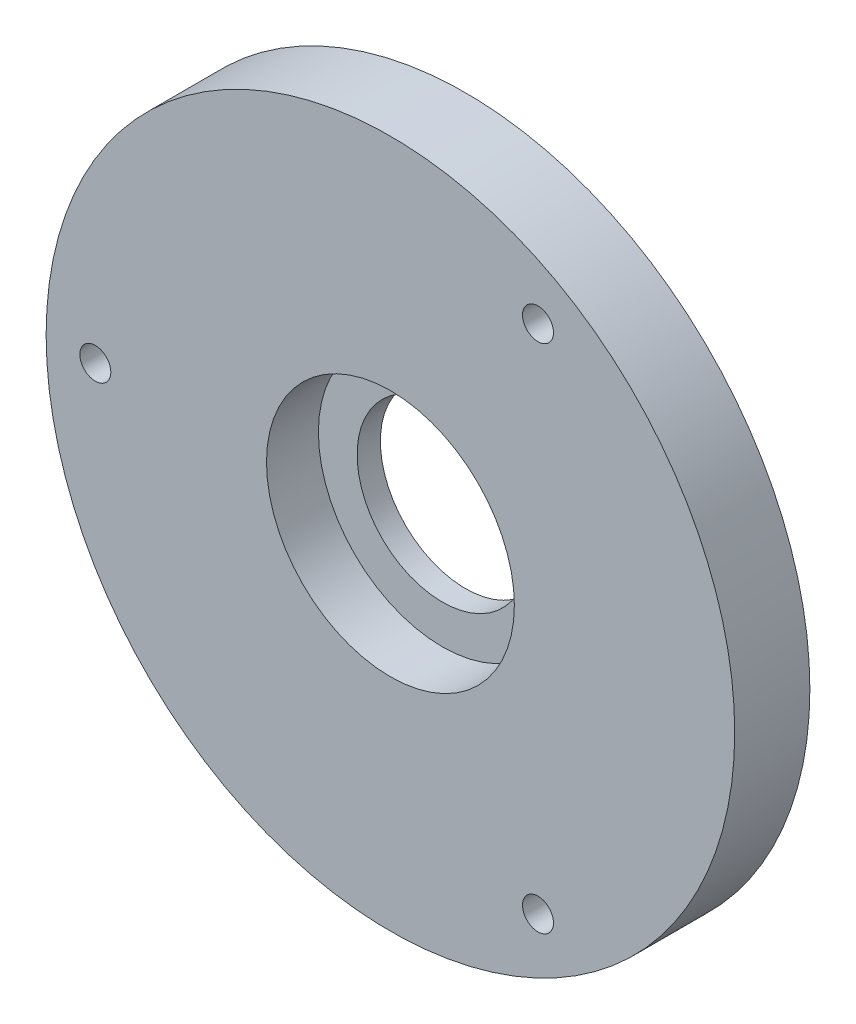
SolidWorks part; units mm, degrees
ref_plane "Front Plane" through (0, 0, 0) normal (0, 0, 1) x (1, 0, 0)
ref_plane "Top Plane" through (0, 0, 0) normal (0, 1, 0) x (1, 0, 0)
ref_plane "Right Plane" through (0, 0, 0) normal (1, 0, 0) x (0, 0, -1)
sketch "Sketch1" plane through (0, 0, 0) normal (0, 0, 1) x (1, 0, 0)
  circle A0 centre (0, 0) radius 44.45
  dimension "D1" = 88.9
extrude "Boss-Extrude1" add sketch "Sketch1" along normal blind 9.7
sketch "Sketch2" plane through (0, 0, 9.7) normal (0, 0, 1) x (1, 0, 0)
  circle A0 centre (0, 0) radius 16
  dimension "D1" = 32
extrude "Cut-Extrude1" cut sketch "Sketch2" against normal offset from surface (6.7 mm away) 3 up to face at (44.45, 0, 0)
sketch "Sketch3" plane through (0, 0, 3) normal (0, 0, 1) x (1, 0, 0)
  circle A0 centre (0, 0) radius 11
  dimension "D1" = 22
extrude "Cut-Extrude2" cut sketch "Sketch3" against normal blind 9
sketch "Sketch5" plane through (0, 0, 0) normal (0, 0, -1) x (-1, 0, 0)
  line L0 (0, 0) -> (38.1, 0) construction
  line L1 (-19.05, 32.9956) -> (0, 0) construction
  line L2 (0, 0) -> (-19.05, -32.9956) construction
  circle A4 centre (38.1, 0) radius 2
  circle A5 centre (-19.05, -32.9956) radius 2
  circle A6 centre (-19.05, 32.9956) radius 2
  circle A7 centre (0, 0) radius 38.1 construction
  dimension "D1" = 120
  dimension "D2" = 120
  dimension "D5" = 4
  dimension "D6" = 76.2
extrude "Cut-Extrude4" cut sketch "Sketch5" against normal through all
